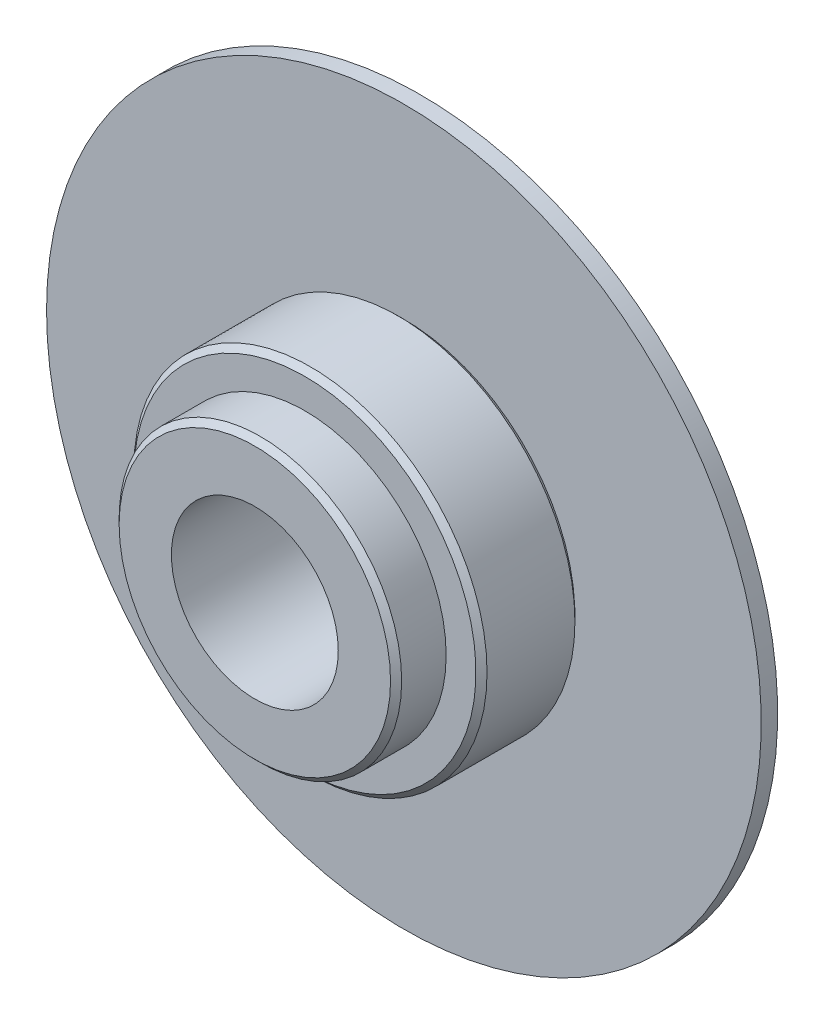
SolidWorks part; units mm, degrees
ref_plane "Front Plane" through (0, 0, 0) normal (0, 0, 1) x (1, 0, 0)
ref_plane "Top Plane" through (0, 0, 0) normal (0, 1, 0) x (1, 0, 0)
ref_plane "Right Plane" through (0, 0, 0) normal (1, 0, 0) x (0, 0, -1)
sketch "Sketch1" plane through (0, 0, 0) normal (0, 0, 1) x (1, 0, 0)
  circle A0 centre (0, 0) radius 5.08
  dimension "D1" = 10.16
extrude "Boss-Extrude1" add sketch "Sketch1" against normal blind 1.8
sketch "Sketch2" plane through (0, 0, -1.8) normal (0, 0, -1) x (-1, 0, 0)
  circle A0 centre (0, 0) radius 6.35
  dimension "D1" = 12.7
extrude "Boss-Extrude2" add sketch "Sketch2" along normal blind 3.56
chamfer "Chamfer1" distance 0.2 angle 45 3 edges at (-6.35, 0, -1.8) (5.08, 0, 0) (-6.35, 0, -5.36)
sketch "Sketch3" plane through (0, 0, -5.36) normal (0, 0, -1) x (-1, 0, 0)
  circle A0 centre (0, 0) radius 12.85
  dimension "D1" = 25.7
extrude "Boss-Extrude3" add sketch "Sketch3" along normal blind 0.59
sketch "Sketch4" plane through (0, 0, -5.95) normal (0, 0, -1) x (-1, 0, 0)
  circle A0 centre (0, 0) radius 5
  dimension "D1" = 10
extrude "Boss-Extrude4" add sketch "Sketch4" along normal blind 0.5
sketch "Sketch5" plane through (0, 0, 0) normal (0, 0, 1) x (1, 0, 0)
  circle A0 centre (0, 0) radius 3
  dimension "D1" = 6
extrude "Cut-Extrude1" cut sketch "Sketch5" against normal through all
